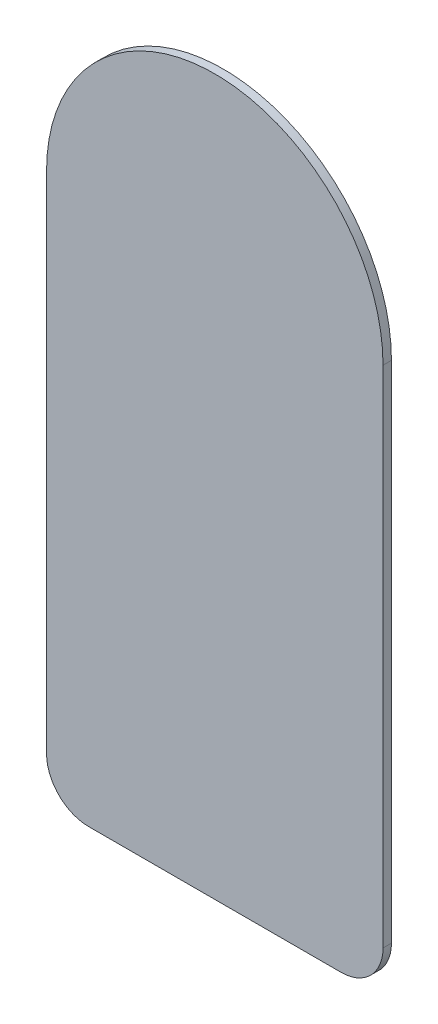
SolidWorks part; units mm, degrees
ref_plane "Front Plane" through (0, 0, 0) normal (0, 0, 1) x (1, 0, 0)
ref_plane "Top Plane" through (0, 0, 0) normal (0, 1, 0) x (1, 0, 0)
ref_plane "Right Plane" through (0, 0, 0) normal (1, 0, 0) x (0, 0, -1)
sketch "Sketch1" plane through (0, 0, 0) normal (0, 0, 1) x (1, 0, 0)
  point P0 (0, 0)
  line B0 (10.16, -30.48) -> (10.16, 0)
  line B1 (-10.16, 0) -> (-10.16, -30.48)
  line B2 (-7.62, -33.02) -> (7.62, -33.02)
  arc B3 (7.62, -33.02) -> (10.16, -30.48) centre (7.62, -30.48) ccw
  arc B4 (10.16, 0) -> (-10.16, 0) centre (0, 0) ccw
  arc B5 (-10.16, -30.48) -> (-7.62, -33.02) centre (-7.62, -30.48) ccw
sketch_block_instance "Block1-1"
sketch_block "Block1"
extrude "Boss-Extrude1" add sketch "Sketch1" along normal blind 0.508
